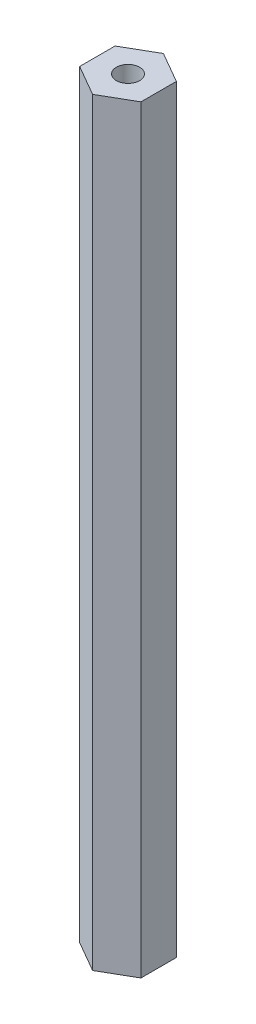
SolidWorks part; units mm, degrees
ref_plane "Front Plane" through (0, 0, 0) normal (0, 0, 1) x (1, 0, 0)
ref_plane "Top Plane" through (0, 0, 0) normal (0, 1, 0) x (1, 0, 0)
ref_plane "Right Plane" through (0, 0, 0) normal (1, 0, 0) x (0, 0, -1)
sketch "Sketch1" plane through (0, 0, 0) normal (0, 1, 0) x (1, 0, 0)
  line L1 (0, 7.3323) -> (-6.35, 3.6662)
  line L2 (-6.35, 3.6662) -> (-6.35, -3.6662)
  line L3 (-6.35, -3.6662) -> (0, -7.3323)
  line L4 (0, -7.3323) -> (6.35, -3.6662)
  line L5 (6.35, -3.6662) -> (6.35, 3.6662)
  line L6 (6.35, 3.6662) -> (0, 7.3323)
  circle A0 centre (0, 0) radius 6.35 construction
  circle A1 centre (0, 0) radius 2.5527 construction
  dimension "D2" = 5.1054
  dimension "D1" = 12.7
extrude "Boss-Extrude1" add sketch "Sketch1" along normal blind 157.1625
hole_wizard "#10-32 Tapped Hole1" positions "3DSketch1" profile "Sketch3" tap size "#10-32" standard "ANSI Inch"
sketch3d "3DSketch1"
  line L1 (-6.35, 157.1625, 0) -> (6.35, 157.1625, 0) construction
  line L2 (-6.35, 157.1625, -3.6662) -> (-6.35, 157.1625, 3.6662) construction
  line L3 (6.35, 157.1625, 3.6662) -> (6.35, 157.1625, -3.6662) construction
  point P3 (0, 157.1625, 0)
  point P11 (0, 0, 0)
sketch "Sketch3" plane through (0, 157.1625, 0) normal (1, 0, 0) x (0, 0, 1)
  line L0 (0, 0) -> (0, 17.9773)
  line L1 (0, 17.9773) -> (2.0193, 16.764)
  line L2 (2.0193, 16.764) -> (2.0193, 12.7)
  line L3 (2.0193, 12.7) -> (2.413, 12.7)
  line L4 (2.413, 12.7) -> (2.413, 0)
  line L5 (2.413, 0) -> (0, 0)
  line L10 (0, 17.9773) -> (-2.0193, 16.764) construction
  line L11 (0, -6.35) -> (0, 107.95) construction
  dimension "Tap Drill Dia." = 4.0386
  dimension "Tap Drill Depth" = 16.764
  dimension "Thread Major Dia." = 4.826
  dimension "Thread Depth" = 12.7
  dimension "Drill Angle" = 118
